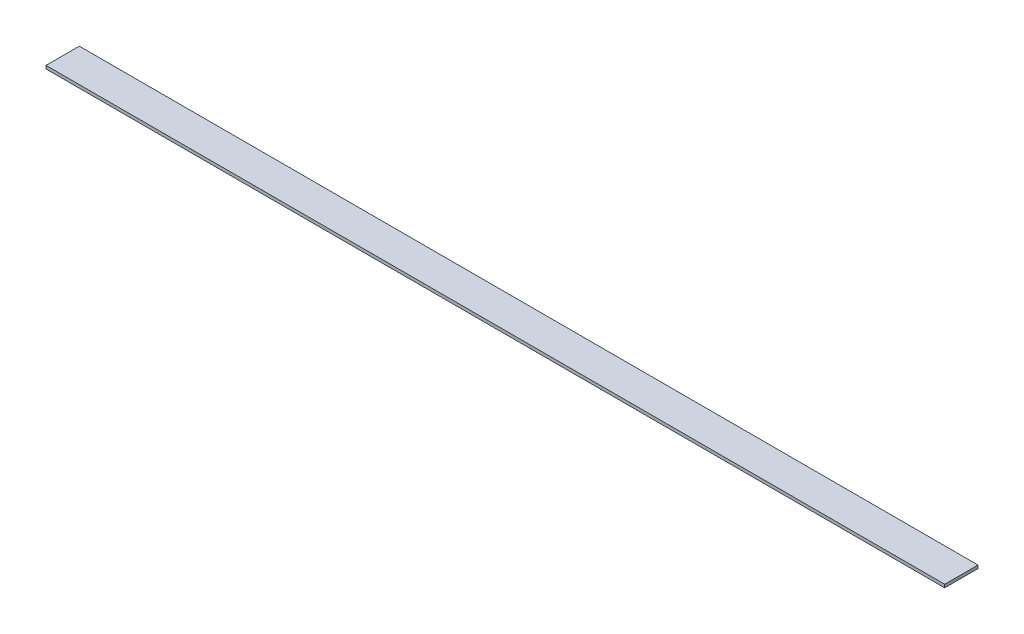
SolidWorks part; units mm, degrees
material "Acrylic (Medium-high impact)"
ref_plane "Front Plane" through (0, 0, 0) normal (0, 0, 1) x (1, 0, 0)
ref_plane "Top Plane" through (0, 0, 0) normal (0, 1, 0) x (1, 0, 0)
ref_plane "Right Plane" through (0, 0, 0) normal (1, 0, 0) x (0, 0, -1)
sketch "Sketch1" plane through (0, 0, 0) normal (0, 1, 0) x (1, 0, 0)
  line L1 (0, 0) -> (917.575, 0)
  line L2 (0, 0) -> (0, 34)
  line L3 (0, 34) -> (917.575, 34)
  line L4 (917.575, 0) -> (917.575, 34)
  dimension "D1" = 917.575
  dimension "D2" = 34
extrude "Boss-Extrude1" add sketch "Sketch1" along normal blind 3.175 contours L2 L3 L4 L1
